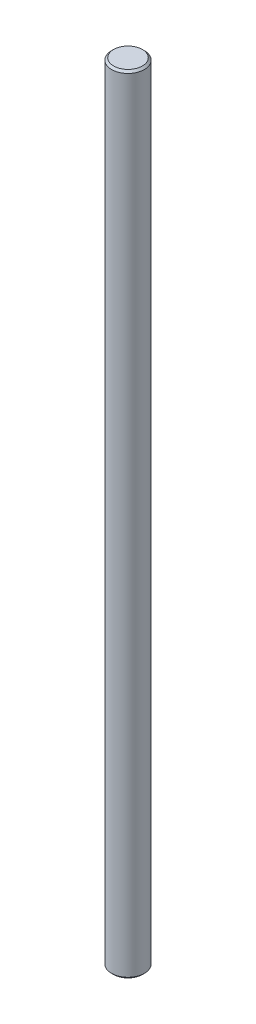
SolidWorks part; units mm, degrees
material "1023 Carbon Steel Sheet (SS)"
ref_plane "Front Plane" through (0, 0, 0) normal (0, 0, 1) x (1, 0, 0)
ref_plane "Top Plane" through (0, 0, 0) normal (0, 1, 0) x (1, 0, 0)
ref_plane "Right Plane" through (0, 0, 0) normal (1, 0, 0) x (0, 0, -1)
sketch "Sketch1" plane through (0, 0, 0) normal (0, 1, 0) x (1, 0, 0)
  circle A0 centre (0, 0) radius 4
  dimension "D1" = 8
extrude "Boss-Extrude1" add sketch "Sketch1" along normal blind 192
chamfer "Chamfer1" distance 0.5 angle 45 2 edges at (0, 192, 4) (0, 0, 4)
